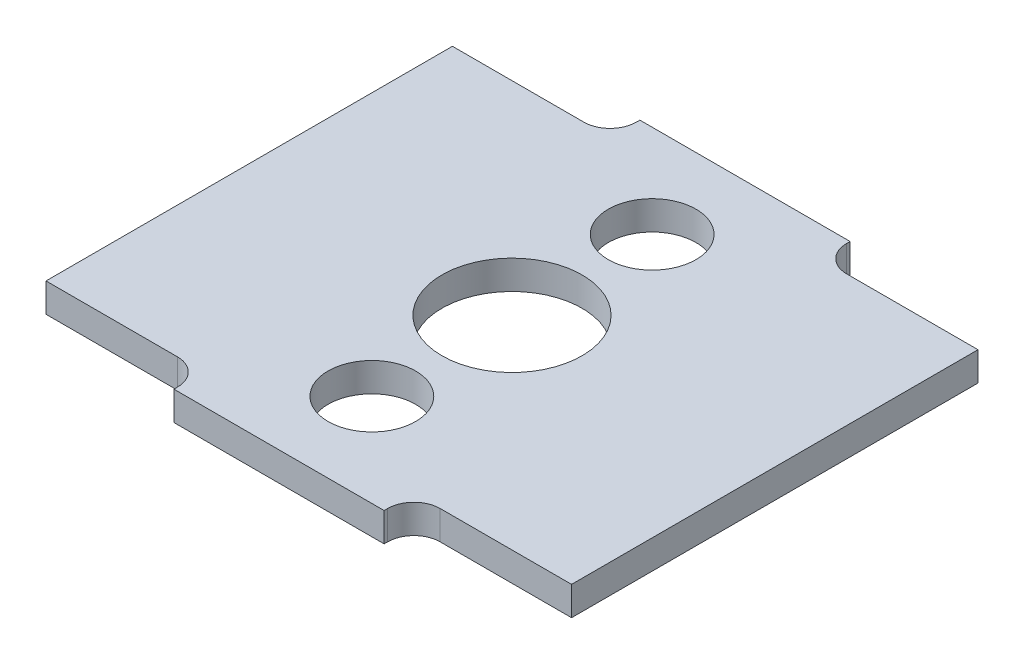
SolidWorks part; units mm, degrees
material "PVC hart"
ref_plane "Ebene vorne" through (0, 0, 0) normal (0, 0, 1) x (1, 0, 0)
ref_plane "Ebene oben" through (0, 0, 0) normal (0, 1, 0) x (1, 0, 0)
ref_plane "Ebene rechts" through (0, 0, 0) normal (1, 0, 0) x (0, 0, -1)
sketch "Skizze1" plane through (0, 0, 0) normal (0, 1, 0) x (1, 0, 0)
  line L1 (-6, 11.6) -> (-6, 13.3)
  line L2 (-6, 13.3) -> (6, 13.3)
  line L3 (6, 13.3) -> (6, 11.6)
  line L5 (15, 11.6) -> (15, -11.6)
  line L7 (-6, -13.3) -> (-6, -11.6)
  line L8 (0, 13.3) -> (0, -13.3) construction
  line L10 (-6, -11.6) -> (-15, -11.6)
  line L13 (0, 8) -> (0, -8) construction
  line L14 (-15, 0) -> (15, 0) construction
  line L15 (6, 11.6) -> (15, 11.6)
  line L16 (-15, 11.6) -> (-15, -11.6)
  line L18 (6, -11.6) -> (15, -11.6)
  line L20 (-6, 11.6) -> (-15, 11.6)
  line L24 (6, -13.3) -> (6, -11.6)
  line L25 (-6, -13.3) -> (6, -13.3)
  line L26 (-6, -11.6) -> (-6, -13.3)
  circle A0 centre (0, -8) radius 1.25
  circle A1 centre (0, 8) radius 1.25
  circle A2 centre (0, 0) radius 5
  point P20 (0, 0)
  dimension "D5" = 23.2
  dimension "D7" = 2.5
  dimension "D9" = 26.6
  dimension "D3" = 16
  dimension "D1" = 10
  dimension "D2" = 12
  dimension "D4" = 30
extrude "Aufsatz-Linear austragen1" add sketch "Skizze1" against normal mid plane 1.65
fillet "Verrundung1" radius 1.5 4 edges at (6, 0, -11.6) (6, 0, 11.6) (-6, 0, 11.6) (-6, 0, -11.6)
sketch "Skizze3" plane through (0, 0.825, 0) normal (0, 1, 0) x (1, 0, 0)
  circle A0 centre (0, 0) radius 4
  circle A1 centre (0, 0) radius 5 construction
  circle A2 centre (0, 0) radius 5
  dimension "D1" = 8
extrude "Aufsatz-Linear austragen2" add sketch "Skizze3" against normal up to surface (1.65 mm away) up to face at (0, -0.825, 5)
sketch "Skizze4" plane through (0, 0.825, 0) normal (0, 1, 0) x (1, 0, 0)
  circle A0 centre (0, 8) radius 2.5
  circle A1 centre (0, -8) radius 2.5
  dimension "D1" = 5
extrude "Schnitt-Linear austragen1" cut sketch "Skizze4" against normal through all
